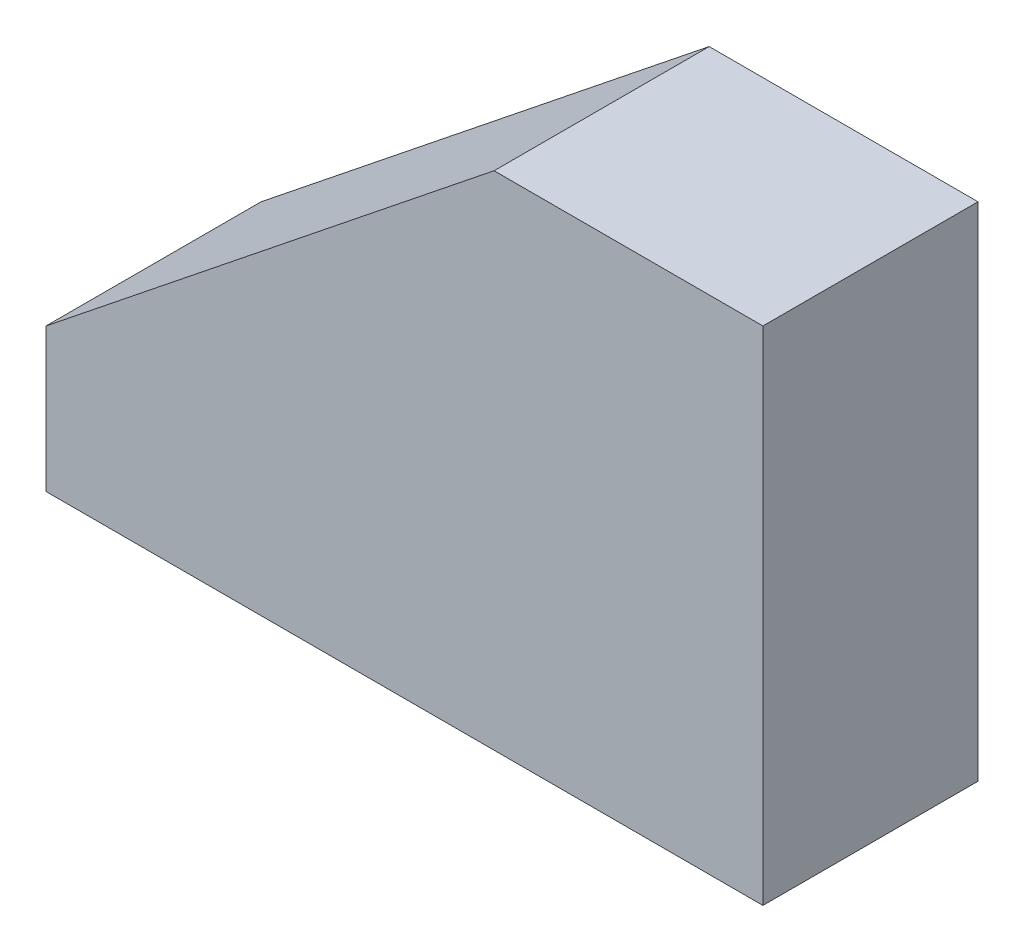
SolidWorks part; units mm, degrees
other "COLL.CONV.HULL-COLL.CONV.HULL-Boss-Extrude2"
ref_plane "Piano frontale" through (0, 0, 0) normal (0, 0, 1) x (1, 0, 0)
ref_plane "Piano superiore" through (0, 0, 0) normal (0, 1, 0) x (1, 0, 0)
ref_plane "Piano destro" through (0, 0, 0) normal (1, 0, 0) x (0, 0, -1)
sketch "Sketch1" plane through (0, 0, 0) normal (0, 1, 0) x (1, 0, 0)
  line L1 (-200, -60) -> (200, -60)
  line L2 (-200, -60) -> (-200, 60)
  line L3 (-200, 60) -> (200, 60)
  line L4 (200, -60) -> (200, 60)
  line L5 (-200, -60) -> (200, 60) construction
  line L6 (-200, 60) -> (200, -60) construction
  point P0 (0, 0)
  dimension "D1" = 120
  dimension "D2" = 400
extrude "Boss-Extrude1" add sketch "Sketch1" along normal mid plane 80
sketch "Sketch3" plane through (0, 0, 60) normal (0, 0, 1) x (1, 0, 0)
  line L0 (-200, 40) -> (50, 240)
  line L1 (50, 240) -> (200, 240)
  line L2 (200, 240) -> (200, 40)
  line L3 (200, 40) -> (-200, 40)
  dimension "D1" = 200
  dimension "D2" = 150
extrude "Boss-Extrude2" add sketch "Sketch3" against normal up to surface (120 mm away) up to face at (0, 0, -60)
sketch "Sketch4" plane through (0, 0, 60) normal (0, 0, 1) x (1, 0, 0)
  line L5 (-200, -40) -> (200, -40)
  line L6 (200, -40) -> (200, 240)
  line L7 (200, 240) -> (50, 240)
  line L8 (50, 240) -> (-200, 40)
  line L9 (-200, 40) -> (-200, -40)
  line L10 (-200, -40) -> (200, -40)
  line L11 (200, -40) -> (200, 240)
  line L12 (200, 240) -> (50, 240)
  line L13 (50, 240) -> (-200, 40)
  line L14 (-200, 40) -> (-200, -40)
  dimension "D1" = 0
extrude "Boss-Extrude3" add sketch "Sketch4" against normal up to surface (120 mm away) separate body up to face at (10, 88, -60)
